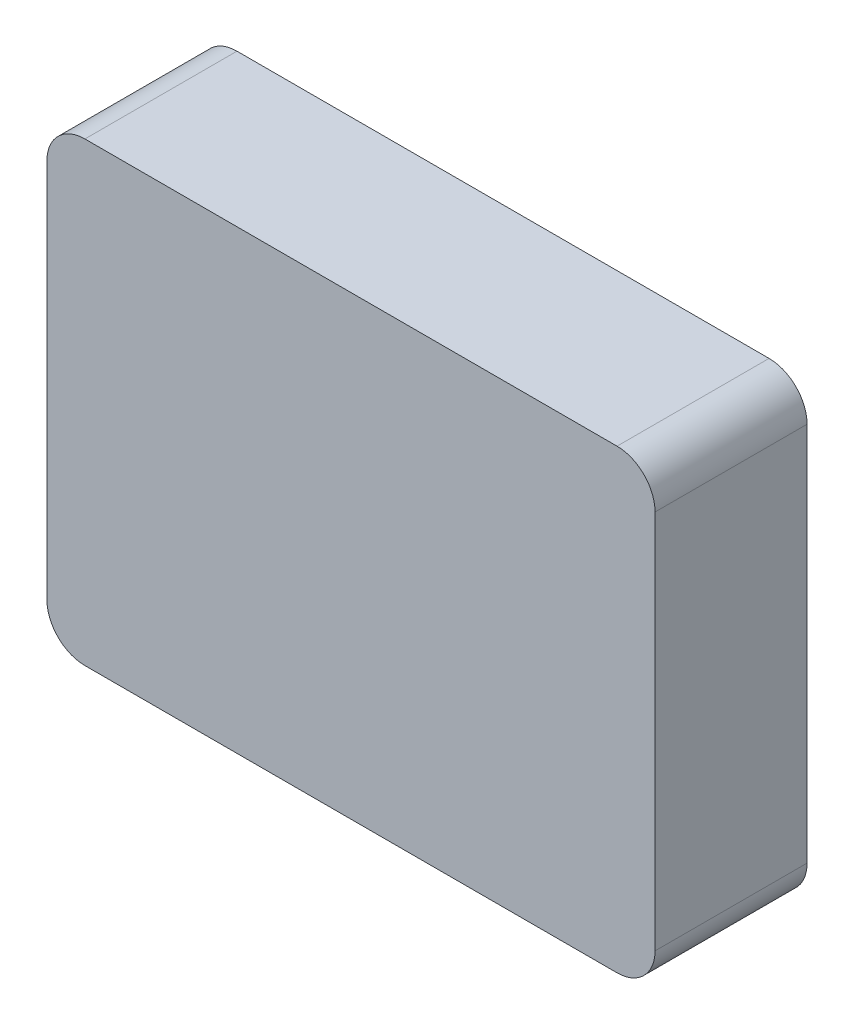
SolidWorks part; units mm, degrees
ref_plane "Plan de face" through (0, 0, 0) normal (0, 0, 1) x (1, 0, 0)
ref_plane "Plan de dessus" through (0, 0, 0) normal (0, 1, 0) x (1, 0, 0)
ref_plane "Plan de droite" through (0, 0, 0) normal (1, 0, 0) x (0, 0, -1)
sketch "Esquisse1" plane through (0, 0, 0) normal (0, 0, 1) x (1, 0, 0)
  line L1 (0, 0) -> (32, 0)
  line L2 (0, 0) -> (0, -24)
  line L3 (0, -24) -> (32, -24)
  line L4 (32, 0) -> (32, -24)
  dimension "D1" = 24
  dimension "D2" = 32
extrude "Boss.-Extru.1" add sketch "Esquisse1" along normal blind 8
fillet "Congé1" radius 2 4 edges at (32, -24, 4) (0, -24, 4) (32, 0, 4) (0, 0, 4)
